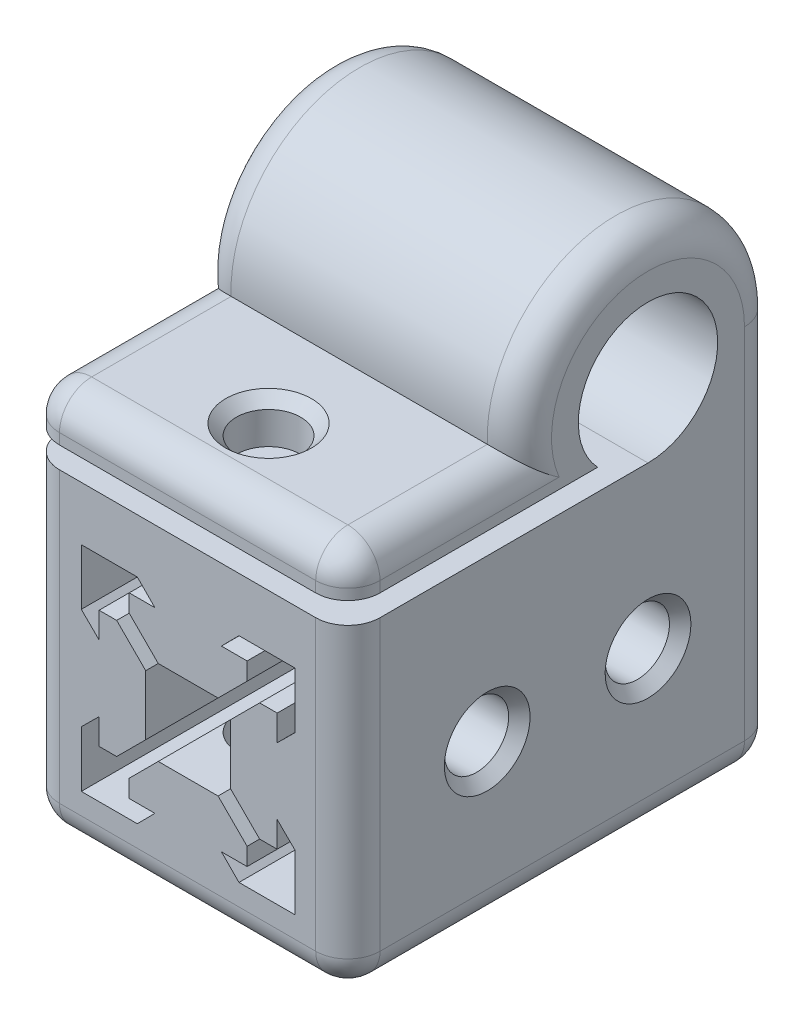
SolidWorks part; units mm, degrees
ref_plane "Front Plane" through (0, 0, 0) normal (0, 0, 1) x (1, 0, 0)
ref_plane "Top Plane" through (0, 0, 0) normal (0, 1, 0) x (1, 0, 0)
ref_plane "Right Plane" through (0, 0, 0) normal (1, 0, 0) x (0, 0, -1)
sketch "Sketch1" plane through (0, 0, 0) normal (0, 0, 1) x (1, 0, 0)
  line L0 (0, -15) -> (0, 15) construction
  line L1 (0, 15) -> (14.8993, 15)
  line L2 (14.8993, 15) -> (14.8993, -14.9496)
  line L3 (14.8993, -14.9496) -> (-15, -14.9496)
  line L4 (-15, -14.9496) -> (-15, 15)
  line L5 (-15, 15) -> (0, 15)
  line L6 (0, -9.9664) -> (0, 9.9664) construction
  line L7 (0, 9.9664) -> (-9.9664, 9.9664) construction
  line L8 (-9.9664, 9.9664) -> (-4.7414, 9.9664)
  line L9 (-4.7414, 9.9664) -> (-3.1, 8.3075)
  line L10 (-3.1, 8.3075) -> (0, 8.3075) construction
  line L11 (-3.1, 8.3075) -> (-5.5, 8.3075)
  line L12 (-5.5, 8.3075) -> (-5.5, 6.6675)
  line L13 (-5.5, 6.6675) -> (-2.79, 3.9575)
  line L14 (-2.79, 3.9575) -> (0, 3.9575) construction
  line L15 (-2.79, 3.9575) -> (2.79, 3.9575)
  line L16 (-9.9664, 9.9664) -> (0, 0) construction
  line L17 (-3.9575, 2.79) -> (-3.9575, -2.79)
  line L18 (-6.6675, 5.5) -> (-3.9575, 2.79)
  line L19 (-8.3075, 5.5) -> (-6.6675, 5.5)
  line L20 (-8.3075, 3.1) -> (-8.3075, 5.5)
  line L21 (-9.9664, 4.7414) -> (-8.3075, 3.1)
  line L22 (-9.9664, 9.9664) -> (-9.9664, 4.7414)
  line L23 (0, 0) -> (-11.0308, 0) construction
  line L24 (5.5, 6.6675) -> (2.79, 3.9575)
  line L25 (5.5, 8.3075) -> (5.5, 6.6675)
  line L26 (3.1, 8.3075) -> (5.5, 8.3075)
  line L27 (4.7414, 9.9664) -> (3.1, 8.3075)
  line L28 (9.9664, 9.9664) -> (4.7414, 9.9664)
  line L29 (9.9664, 9.9664) -> (9.9664, 4.7414)
  line L30 (9.9664, 4.7414) -> (8.3075, 3.1)
  line L31 (8.3075, 3.1) -> (8.3075, 5.5)
  line L32 (8.3075, 5.5) -> (6.6675, 5.5)
  line L33 (6.6675, 5.5) -> (3.9575, 2.79)
  line L34 (3.9575, 2.79) -> (3.9575, -2.79)
  line L35 (-9.9664, -9.9664) -> (0, 0) construction
  line L36 (-2.79, -3.9575) -> (0, -3.9575) construction
  line L37 (-3.1, -8.3075) -> (0, -8.3075) construction
  line L38 (0, -9.9664) -> (-9.9664, -9.9664) construction
  line L39 (6.6675, -5.5) -> (3.9575, -2.79)
  line L40 (8.3075, -5.5) -> (6.6675, -5.5)
  line L41 (8.3075, -3.1) -> (8.3075, -5.5)
  line L42 (9.9664, -4.7414) -> (8.3075, -3.1)
  line L43 (9.9664, -9.9664) -> (9.9664, -4.7414)
  line L44 (9.9664, -9.9664) -> (4.7414, -9.9664)
  line L45 (4.7414, -9.9664) -> (3.1, -8.3075)
  line L46 (3.1, -8.3075) -> (5.5, -8.3075)
  line L47 (5.5, -8.3075) -> (5.5, -6.6675)
  line L48 (5.5, -6.6675) -> (2.79, -3.9575)
  line L49 (-9.9664, -9.9664) -> (-9.9664, -4.7414)
  line L50 (-9.9664, -4.7414) -> (-8.3075, -3.1)
  line L51 (-8.3075, -3.1) -> (-8.3075, -5.5)
  line L52 (-8.3075, -5.5) -> (-6.6675, -5.5)
  line L53 (-6.6675, -5.5) -> (-3.9575, -2.79)
  line L54 (-2.79, -3.9575) -> (2.79, -3.9575)
  line L55 (-5.5, -6.6675) -> (-2.79, -3.9575)
  line L56 (-5.5, -8.3075) -> (-5.5, -6.6675)
  line L57 (-3.1, -8.3075) -> (-5.5, -8.3075)
  line L58 (-4.7414, -9.9664) -> (-3.1, -8.3075)
  line L59 (-9.9664, -9.9664) -> (-4.7414, -9.9664)
  point P43 (3.9575, 0)
  point P58 (-3.9575, 0)
  dimension "D1" = 3.1
  dimension "D2" = 2.79
  dimension "D3" = 2.4
  dimension "D4" = 135
  dimension "D5" = 1.64
  dimension "D6" = 15
  dimension "D7" = 15
  dimension "D8" = 9.9664
  dimension "D9" = 5.225
extrude "Boss-Extrude1" add sketch "Sketch1" along normal blind 40
sketch "Sketch5" plane through (-15, 0, 0) normal (-1, 0, 0) x (0, 0, 1)
  line L0 (0, 15) -> (12, 15) construction
  line L1 (40, 15) -> (0, 15) construction
  line L2 (12, 15) -> (12, 21.5) construction
  line L3 (0, 21.5) -> (0, 15)
  line L4 (0, 15) -> (12, 15)
  line L5 (23.9896, 21) -> (40, 21)
  line L6 (40, 21) -> (40, 17)
  line L7 (40, 17) -> (27.8045, 17)
  line L8 (27.8045, 17) -> (16.6904, 17)
  arc A0 (0, 21.5) -> (23.9896, 21) centre (12, 21.5) cw
  arc A1 (12, 15) -> (16.6904, 17) centre (12, 21.5) cw
  dimension "D3" = 12
  dimension "D1" = 2
  dimension "D2" = 4
  dimension "D4" = 6.5
extrude "Boss-Extrude3" add sketch "Sketch5" against normal through all
sketch "Sketch3" plane through (-15, 0, 0) normal (-1, 0, 0) x (0, 0, 1)
  line L0 (12, 0) -> (40, 0.0252) construction
  line L2 (0, 0) -> (12, 0) construction
  line L3 (40, 15) -> (40, -14.9496) construction
  circle A0 centre (12, 0) radius 3
  circle A1 centre (27, 0) radius 3
  dimension "D1" = 15
extrude "Cut-Extrude1" cut sketch "Sketch3" against normal through all
sketch "Sketch4" plane through (0, 22.0582, 0) normal (0, 1, 0) x (1, 0, 0)
  line L0 (-15, -40) -> (-15, -23.9896) construction
  line L2 (14.8993, -40) -> (-15, -40) construction
  circle A0 centre (0, -32.5) radius 3
  dimension "D1" = 15
  dimension "D2" = 7.5
extrude "Cut-Extrude2" cut sketch "Sketch4" against normal through all
fillet "Fillet1" radius 3 15 edges at (-15, 33.4974, 12.2501) (14.8993, 33.4974, 12.2501) (-0.0504, -14.9496, 40) (-15, 21, 31.9948) (14.8993, 21, 31.9948) (-0.0504, 21, 40) (-15, 19, 40) (14.8993, 19, 40) (14.8993, 0.0252, 40) (-15, 0.0252, 40) (14.8993, 3.2752, 0) (-15, 3.2752, 0) (-0.0504, -14.9496, 0) (14.8993, -14.9496, 20) (-15, -14.9496, 20)
chamfer "Chamfer1" distance 1 angle 45 6 edges at (0, -14.9496, 35.5) (14.8993, 0, 30) (14.8993, 0, 15) (-15, 0, 15) (-15, 0, 30) (0, 21, 35.5)
